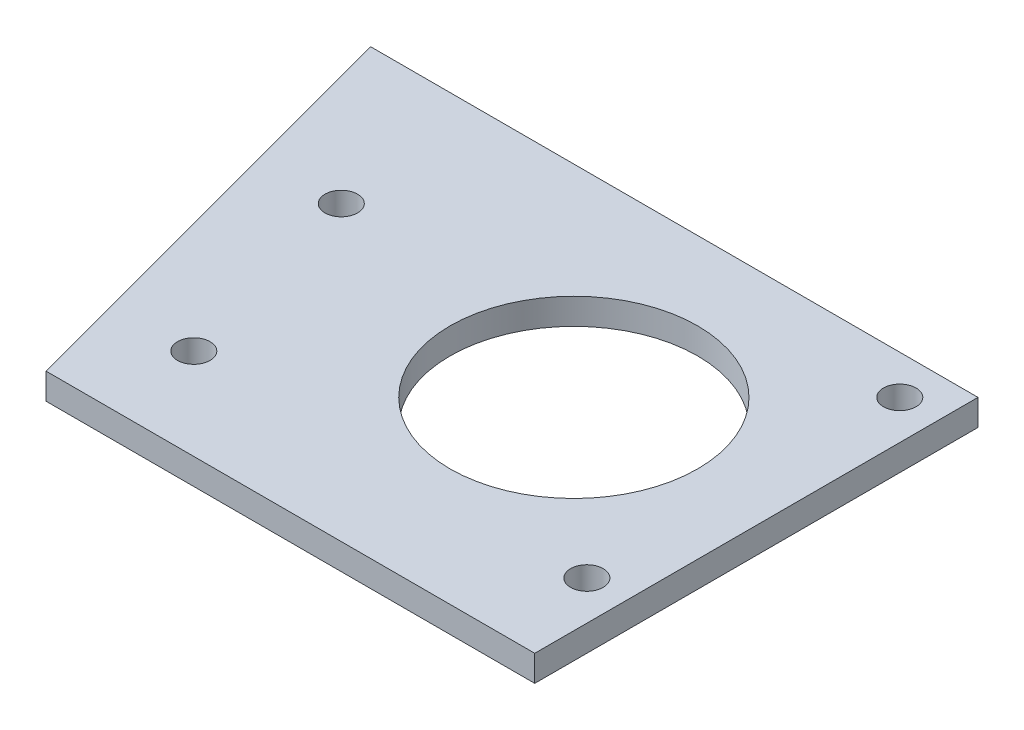
SolidWorks part; units mm, degrees
material "1.0553 (S355J0)"
ref_plane "Płaszczyzna przednia" through (0, 0, 0) normal (0, 0, 1) x (1, 0, 0)
ref_plane "Płaszczyzna górna" through (0, 0, 0) normal (0, 1, 0) x (1, 0, 0)
ref_plane "Płaszczyzna prawa" through (0, 0, 0) normal (1, 0, 0) x (0, 0, -1)
sketch "Szkic1" plane through (0, 0, 0) normal (0, 1, 0) x (1, 0, 0)
  line L1 (-463.5553, -566.5676) -> (463.5553, -566.5676)
  line L2 (-463.5553, -566.5676) -> (-463.5553, 566.5676)
  line L3 (-463.5553, 566.5676) -> (463.5553, 566.5676)
  line L4 (463.5553, -566.5676) -> (463.5553, 566.5676)
  point P4 (0, 566.5676)
  point P6 (-463.5553, 0)
sketch "Szkic2" [suppressed] plane through (0, 0, 0) normal (0, 1, 0) x (1, 0, 0)
  line L1 (-65, 65) -> (65, 65)
  line L2 (-65, 65) -> (-65, -65)
  line L3 (-65, -65) -> (65, -65)
  line L4 (65, 65) -> (65, -65)
  circle A0 centre (0, 0) radius 37.5
  circle A1 centre (0, -53) radius 5.25
  point P12 (65, 0)
  point P15 (0, 65)
  dimension "D2" = 10.5
  dimension "D3" = 75
  dimension "D1" = 53
  dimension "D4" = 130
  dimension "D5" = 130
extrude "Dodanie-wyciągnięcie1" [suppressed] add sketch "Szkic2" along normal blind 10
pattern_circular "Szyk kołowy1" [suppressed] count 4 every 90
chamfer "Sfazowanie1" [suppressed] distance 20 angle 45
sketch "Szkic3" plane through (0, 0, 0) normal (0, 1, 0) x (1, 0, 0)
  line L3 (-77.5, 77.5) -> (77.5, 77.5)
  line L4 (77.5, -77.5) -> (77.5, 77.5)
  line L6 (-109.9486, -92.5) -> (-155.5, 77.5)
  line L7 (-155.5, 77.5) -> (-77.5, 77.5)
  line L8 (-109.9486, -92.5) -> (-270.1261, -92.5) construction
  line L9 (77.5, -77.5) -> (77.5, -92.5)
  line L10 (77.5, -92.5) -> (-109.9486, -92.5)
  line L11 (-108.9741, 19.7741) -> (-88.2686, -57.5) construction
  line L12 (-88.2686, -57.5) -> (-117.2463, -65.2646) construction
  circle A0 centre (0, 0) radius 47.5
  circle A1 centre (62.5, 62.5) radius 6.25
  circle A2 centre (62.5, -57.5) radius 6.25
  circle A3 centre (-88.2686, -57.5) radius 6.25
  circle A4 centre (-108.9741, 19.7741) radius 6.25
  point P4 (0, 77.5)
  point P6 (77.5, 0)
  dimension "D1" = 95
  dimension "D7" = 12.5
  dimension "D10" = 120
  dimension "D2" = 155
  dimension "D3" = 155
  dimension "D4" = 15
  dimension "D5" = 78
  dimension "D6" = 75
  dimension "D8" = 15
  dimension "D9" = 15
  dimension "D11" = 30
  dimension "D12" = 80
extrude "Dodanie-wyciągnięcie2" add sketch "Szkic3" along normal blind 10
sketch "Szkic4" [suppressed] plane through (0, 10, 0) normal (0, 1, 0) x (1, 0, 0)
  line L0 (-55, 55) -> (55, -55) construction
  line L1 (-45, 65) -> (-65, 45) construction
  line L2 (45, -65) -> (65, -45) construction
  line L3 (55, 55) -> (-55, -55) construction
  line L4 (65, 45) -> (45, 65) construction
  line L5 (-65, -45) -> (-45, -65) construction
